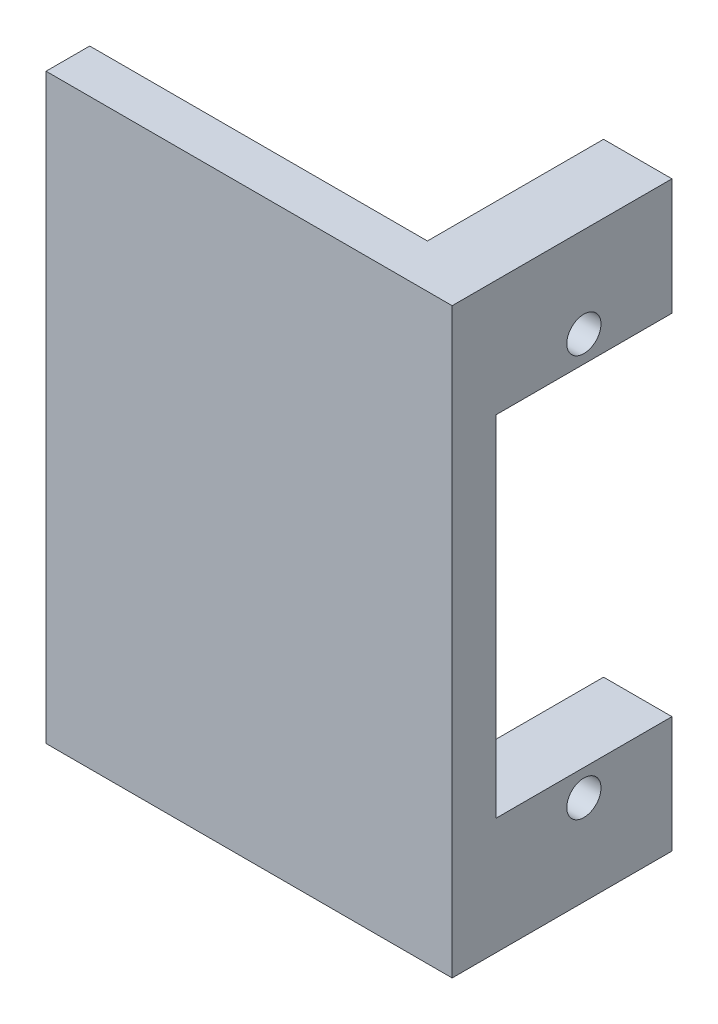
SolidWorks part; units mm, degrees
ref_plane "Front Plane" through (0, 0, 0) normal (0, 0, 1) x (1, 0, 0)
ref_plane "Top Plane" through (0, 0, 0) normal (0, 1, 0) x (1, 0, 0)
ref_plane "Right Plane" through (0, 0, 0) normal (1, 0, 0) x (0, 0, -1)
sketch "Sketch1" plane through (0, 0, 0) normal (0, 1, 0) x (1, 0, 0)
  line L0 (0, 12.1) -> (4.7, 12.1)
  line L1 (4.7, 12.1) -> (4.7, -3)
  line L2 (4.7, -3) -> (-23.2, -3)
  line L3 (-23.2, -3) -> (-23.2, 0)
  line L4 (-23.2, 0) -> (0, 0)
  line L5 (0, 12.1) -> (0, 0)
  point P2 (6.413, -4.3572)
  point P7 (0, 0)
  point P8 (4.7, 4.536)
  dimension "D1" = 3
  dimension "D2" = 4.7
  dimension "D3" = 23.2
  dimension "D4" = 12.1
extrude "Boss-Extrude1" add sketch "Sketch1" along normal blind 40
sketch "Sketch2" plane through (4.7, 0, 0) normal (1, 0, 0) x (0, 0, -1)
  line L0 (12.1, 40) -> (12.1, 0) construction
  line L1 (0, 32) -> (12.1, 32)
  line L2 (0, 32) -> (0, 8)
  line L3 (0, 8) -> (12.1, 8)
  line L4 (12.1, 32) -> (12.1, 8)
  line L5 (0, 32) -> (12.1, 8) construction
  line L6 (0, 8) -> (12.1, 32) construction
  line L7 (12.1, 40) -> (0, 40) construction
  line L8 (-3, 40) -> (-3, 0) construction
  point P0 (6.05, 20)
  point P5 (0, 0)
  point P8 (12.1, 20)
  point P11 (6.05, 40)
  dimension "D1" = 3
  dimension "D2" = 24
sketch "Sketch3" plane through (0, 0, 0) normal (0, 0, -1) x (-1, 0, 0)
  line L0 (23.2, 40) -> (23.2, 0) construction
  line L1 (21.6, 11.5) -> (1.6, 11.5)
  line L2 (21.6, 11.5) -> (21.6, 28.5)
  line L3 (21.6, 28.5) -> (1.6, 28.5)
  line L4 (1.6, 11.5) -> (1.6, 28.5)
  line L5 (21.6, 11.5) -> (1.6, 28.5) construction
  line L6 (21.6, 28.5) -> (1.6, 11.5) construction
  line L7 (0, 40) -> (23.2, 40) construction
  point P0 (11.6, 20)
  point P5 (11.5621, 19.4843)
  point P6 (0, 0)
  point P9 (23.2, 20)
  point P12 (11.6, 40)
  dimension "D1" = 20
  dimension "D2" = 17
extrude "Cut-Extrude3" cut sketch "Sketch2" against normal up to surface (4.7 mm away) up to face at (0, 20, -6.05)
sketch "Sketch4" plane through (4.7, 0, 0) normal (1, 0, 0) x (0, 0, -1)
  line L0 (6.05, 33.8) -> (6.05, 6.2) construction
  line L1 (-3, 40) -> (-3, 0) construction
  line L2 (12.1, 40) -> (12.1, 32) construction
  circle A0 centre (6.05, 33.8) radius 1.175
  circle A1 centre (6.05, 6.2) radius 1.175
  point P5 (5.1379, 1.4885)
  point P7 (-3, 20)
  point P8 (6.05, 20)
  dimension "D2" = 2.35
  dimension "D1" = 27.6
  dimension "D3" = 6.05
extrude "Cut-Extrude4" cut sketch "Sketch4" against normal up to surface (4.7 mm away) up to face at (0, 36, -6.05)
